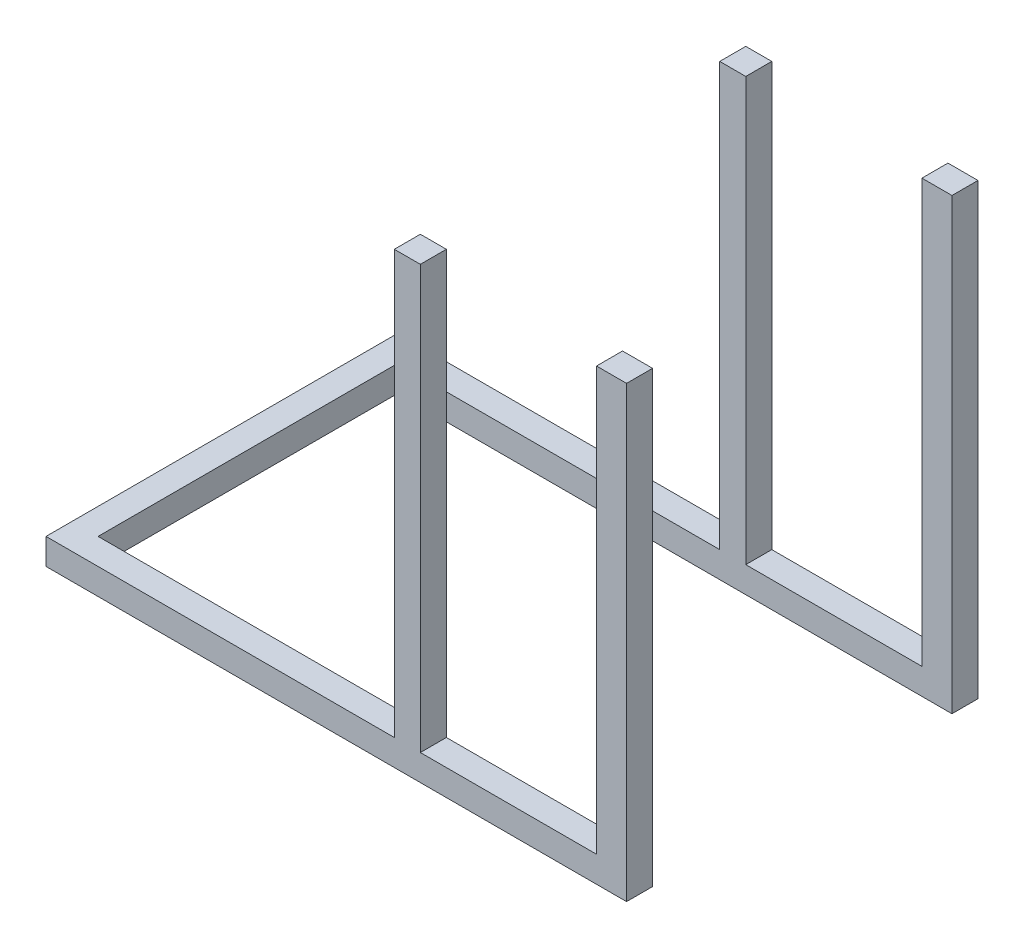
SolidWorks part; units mm, degrees
ref_plane "Alzado" through (0, 0, 0) normal (0, 0, 1) x (1, 0, 0)
ref_plane "Planta" through (0, 0, 0) normal (0, 1, 0) x (1, 0, 0)
ref_plane "Vista lateral" through (0, 0, 0) normal (1, 0, 0) x (0, 0, -1)
sketch "Croquis2" plane through (0, 0, 0) normal (0, 1, 0) x (1, 0, 0)
  line L0 (858.4, -333.5) -> (858.4, -391.5)
  line L1 (-435, 391.5) -> (858.4, 391.5)
  line L2 (-435, 391.5) -> (-435, -391.5)
  line L3 (-435, -391.5) -> (858.4, -391.5)
  line L4 (858.4, 391.5) -> (858.4, 333.5)
  line L5 (-377, 333.5) -> (858.4, 333.5)
  line L6 (-377, 333.5) -> (-377, -333.5)
  line L7 (-377, -333.5) -> (858.4, -333.5)
  point P11 (-309.024, -391.5)
  dimension "D1" = 58
  dimension "D2" = 58
  dimension "D3" = 58
  dimension "D4" = 783
  dimension "D5" = 435
extrude "Saliente-Extruir1" add sketch "Croquis2" along normal blind 58
sketch "Croquis3" plane through (0, 0, 0) normal (0, 1, 0) x (1, 0, 0)
  line L0 (858.4, 391.5) -> (-435, 391.5) construction
  line L1 (399, 391.5) -> (341, 391.5)
  line L2 (399, 391.5) -> (399, 333.5)
  line L3 (399, 333.5) -> (341, 333.5)
  line L4 (341, 391.5) -> (341, 333.5)
  line L5 (-377, 333.5) -> (858.4, 333.5) construction
  line L6 (-435, -391.5) -> (858.4, -391.5) construction
  line L7 (858.4, 391.5) -> (791.4523, 391.5)
  line L8 (858.4, 391.5) -> (858.4, 333.5)
  line L9 (858.4, 333.5) -> (791.4523, 333.5)
  line L10 (791.4523, 391.5) -> (791.4523, 333.5)
  line L11 (858.4, -333.5) -> (791.4523, -333.5)
  line L12 (858.4, -333.5) -> (858.4, -391.5)
  line L13 (858.4, -391.5) -> (791.4523, -391.5)
  line L14 (791.4523, -333.5) -> (791.4523, -391.5)
  line L15 (858.4, -333.5) -> (-377, -333.5) construction
  line L16 (341, -333.5) -> (399, -333.5)
  line L17 (341, -333.5) -> (341, -391.5)
  line L18 (341, -391.5) -> (399, -391.5)
  line L19 (399, -333.5) -> (399, -391.5)
  line L20 (-435, 391.5) -> (-435, -391.5) construction
  dimension "D1" = 834
  dimension "D2" = 58
  dimension "D3" = 834
extrude "Saliente-Extruir2" add sketch "Croquis3" along normal blind 1000
